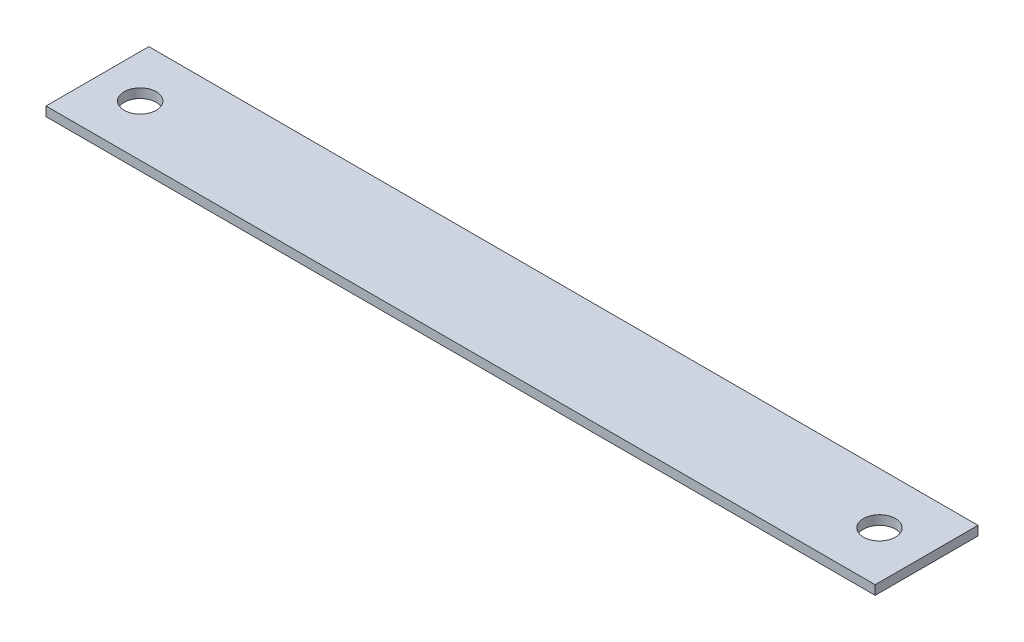
SolidWorks part; units mm, degrees
ref_plane "Front Plane" through (0, 0, 0) normal (0, 0, 1) x (1, 0, 0)
ref_plane "Top Plane" through (0, 0, 0) normal (0, 1, 0) x (1, 0, 0)
ref_plane "Right Plane" through (0, 0, 0) normal (1, 0, 0) x (0, 0, -1)
sketch "Sketch1" plane through (0, 0, 0) normal (0, 1, 0) x (1, 0, 0)
  line L1 (0, 0) -> (204.7875, 0)
  line L2 (0, 0) -> (0, 25.4)
  line L3 (0, 25.4) -> (204.7875, 25.4)
  line L4 (204.7875, 0) -> (204.7875, 25.4)
  dimension "D1" = 204.7875
  dimension "D2" = 25.4
extrude "Boss-Extrude1" add sketch "Sketch1" along normal blind 2.286
sketch "Sketch2" plane through (0, 2.286, 0) normal (0, 1, 0) x (1, 0, 0)
  line L0 (0, 25.4) -> (0, 0) construction
  line L1 (204.7875, 0) -> (204.7875, 25.4) construction
  circle A0 centre (10.5664, 12.7) radius 3.9688
  circle A1 centre (193.1543, 12.7) radius 3.9687
  point P8 (0, 12.7)
  dimension "D1" = 7.9375
  dimension "D2" = 10.5664
  dimension "D3" = 11.6332
  dimension "D4" = 7.9375
extrude "Cut-Extrude1" cut sketch "Sketch2" against normal through all
